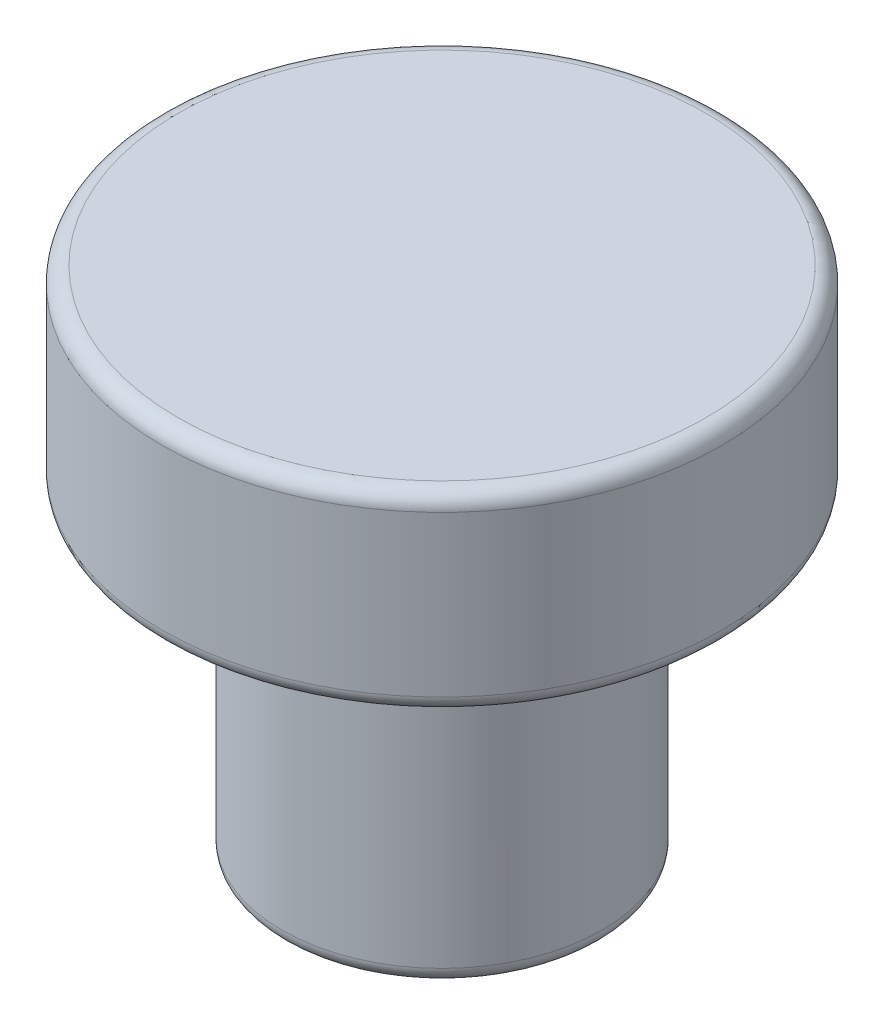
SolidWorks part; units mm, degrees
ref_plane "Front Plane" through (0, 0, 0) normal (0, 0, 1) x (1, 0, 0)
ref_plane "Top Plane" through (0, 0, 0) normal (0, 1, 0) x (1, 0, 0)
ref_plane "Right Plane" through (0, 0, 0) normal (1, 0, 0) x (0, 0, -1)
sketch "Sketch1" plane through (0, 0, 0) normal (0, 1, 0) x (1, 0, 0)
  circle A0 centre (0, 0) radius 17.5
  dimension "D1" = 35
extrude "Boss-Extrude1" add sketch "Sketch1" along normal blind 12
sketch "Sketch2" plane through (0, 0, 0) normal (0, -1, 0) x (1, 0, 0)
  circle A0 centre (0, 0) radius 10
  dimension "D1" = 20
extrude "Boss-Extrude2" add sketch "Sketch2" along normal blind 20 contours A0
fillet "Fillet1" radius 1 4 edges at (0, -20, -10) (0, 0, -10) (0, 0, 17.5) (0, 12, 17.5)
